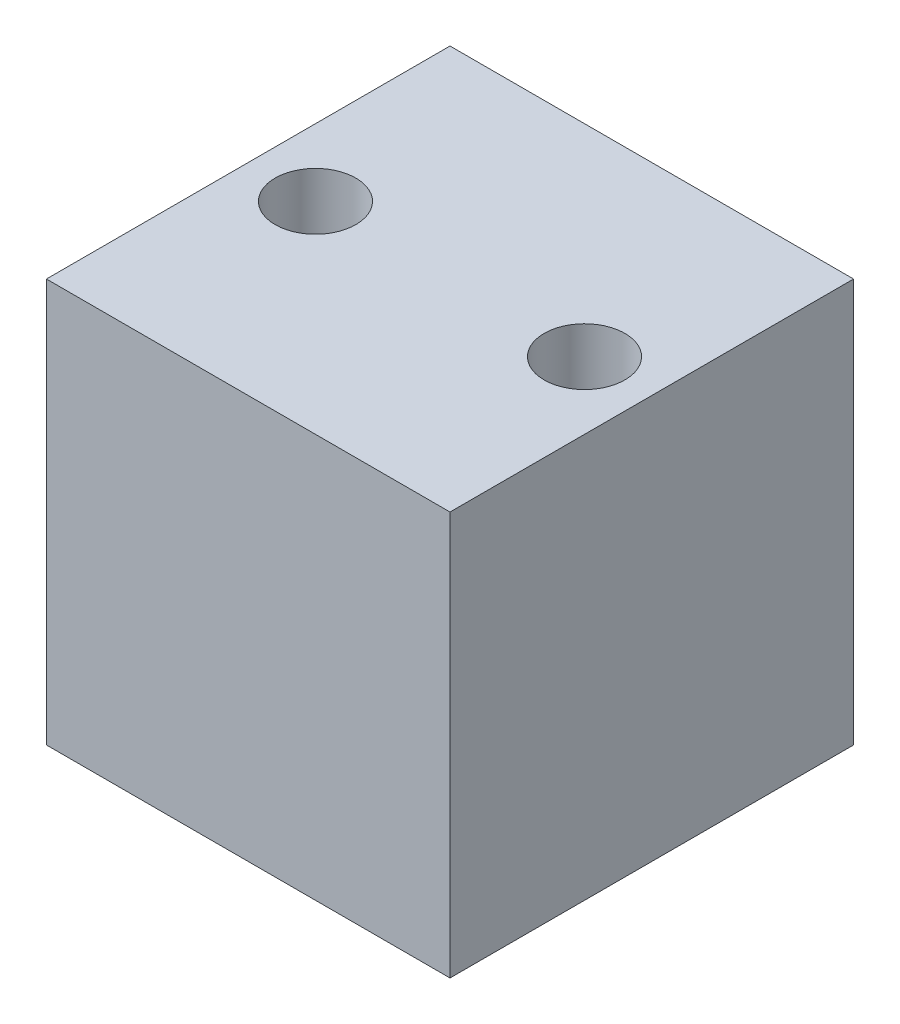
SolidWorks part; units mm, degrees
ref_plane "Front Plane" through (0, 0, 0) normal (0, 0, 1) x (1, 0, 0)
ref_plane "Top Plane" through (0, 0, 0) normal (0, 1, 0) x (1, 0, 0)
ref_plane "Right Plane" through (0, 0, 0) normal (1, 0, 0) x (0, 0, -1)
sketch "Sketch1" plane through (0, 0, 0) normal (0, 1, 0) x (1, 0, 0)
  line L1 (-38.1, 38.1) -> (0, 38.1)
  line L2 (-38.1, 38.1) -> (-38.1, 0)
  line L3 (-38.1, 0) -> (0, 0)
  line L4 (0, 38.1) -> (0, 0)
  circle A1 centre (-31.75, 19.05) radius 3.81
  circle A2 centre (-6.35, 19.05) radius 3.81
  dimension "D3" = 7.62
  dimension "D4" = 7.62
  dimension "D1" = 38.1
  dimension "D2" = 38.1
  dimension "D6" = 19.05
  dimension "D7" = 6.35
  dimension "D8" = 6.35
extrude "Boss-Extrude1" add sketch "Sketch1" along normal blind 38.1
